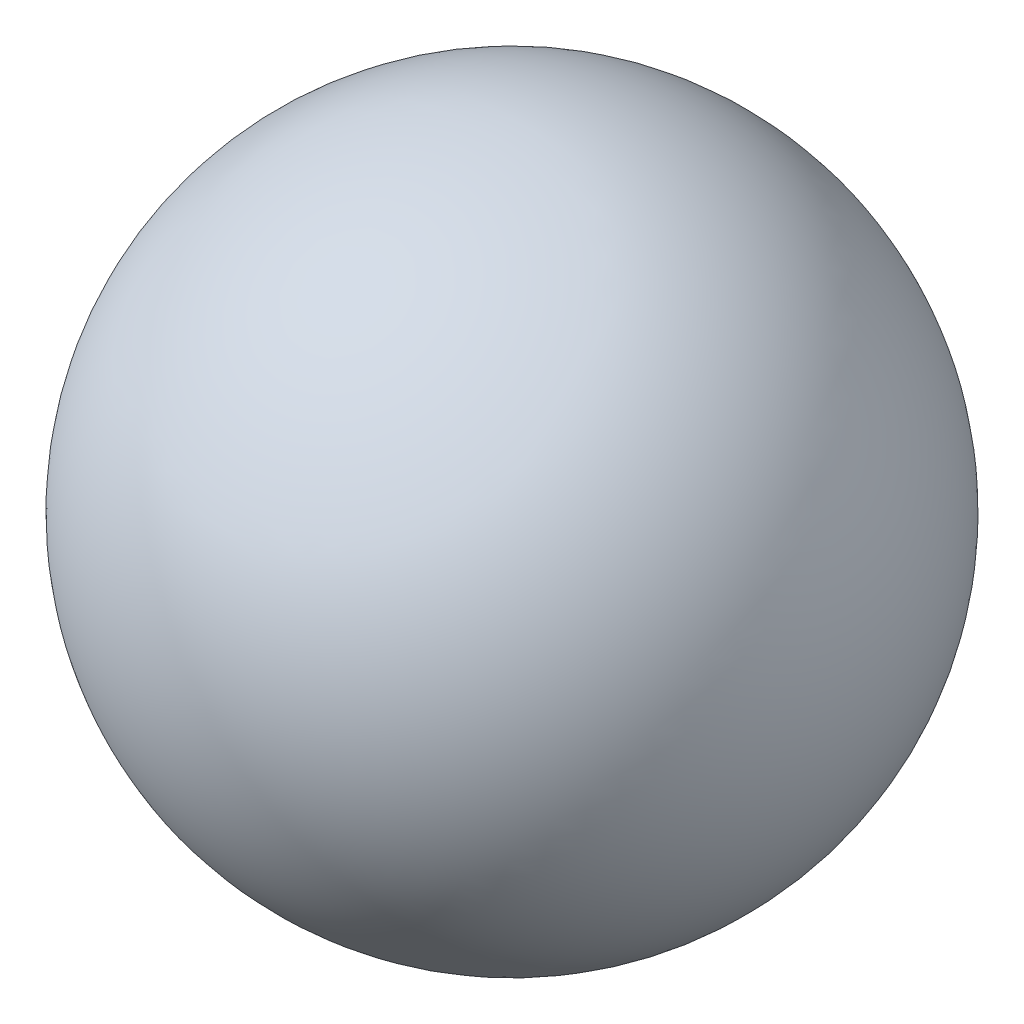
SolidWorks part; units mm, degrees
ref_plane "Front Plane" through (0, 0, 0) normal (0, 0, 1) x (1, 0, 0)
ref_plane "Top Plane" through (0, 0, 0) normal (0, 1, 0) x (1, 0, 0)
ref_plane "Right Plane" through (0, 0, 0) normal (1, 0, 0) x (0, 0, -1)
sketch "Sketch2" plane through (0, 0, 0) normal (0, 1, 0) x (1, 0, 0)
  line L0 (0, 3.175) -> (0, -1.5875) construction
  line L1 (0, 3.175) -> (0, -1.5875)
  arc A1 (0, 3.175) -> (0, -1.5875) centre (0, 0.7937) cw
  dimension "D1" = 4.7625
revolve "Revolve11" add sketch "Sketch2" angle 360 about L0
